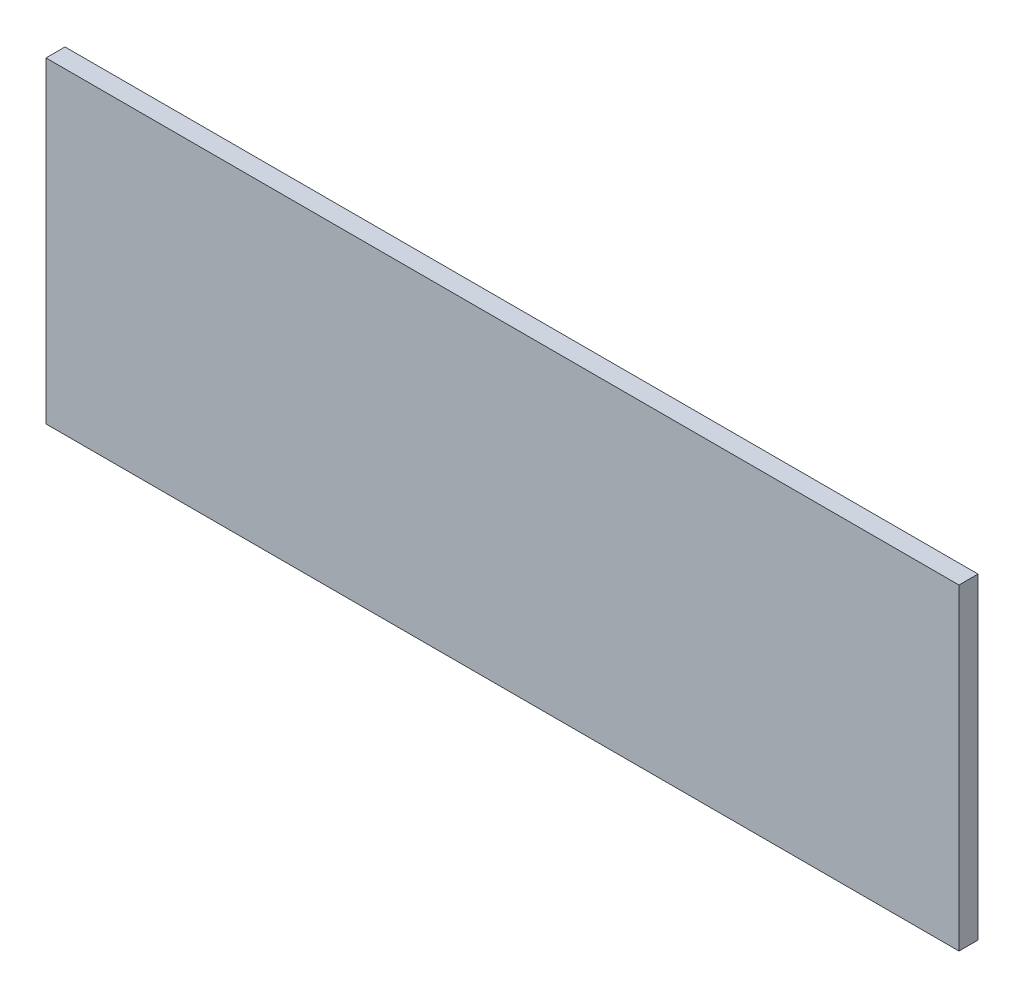
SolidWorks part; units mm, degrees
ref_plane "Front Plane" through (0, 0, 0) normal (0, 0, 1) x (1, 0, 0)
ref_plane "Top Plane" through (0, 0, 0) normal (0, 1, 0) x (1, 0, 0)
ref_plane "Right Plane" through (0, 0, 0) normal (1, 0, 0) x (0, 0, -1)
sketch "Sketch1" plane through (0, 0, 0) normal (0, 0, 1) x (1, 0, 0)
  line L1 (-72, 25) -> (72, 25)
  line L2 (-72, 25) -> (-72, -25)
  line L3 (-72, -25) -> (72, -25)
  line L4 (72, 25) -> (72, -25)
  line L6 (72, 25) -> (-72, 25) construction
  point P4 (0, -25)
  point P6 (-72, 0)
  point P7 (0, 0)
  point P8 (64.2861, -25)
extrude "Boss-Extrude1" add sketch "Sketch1" along normal blind 3
